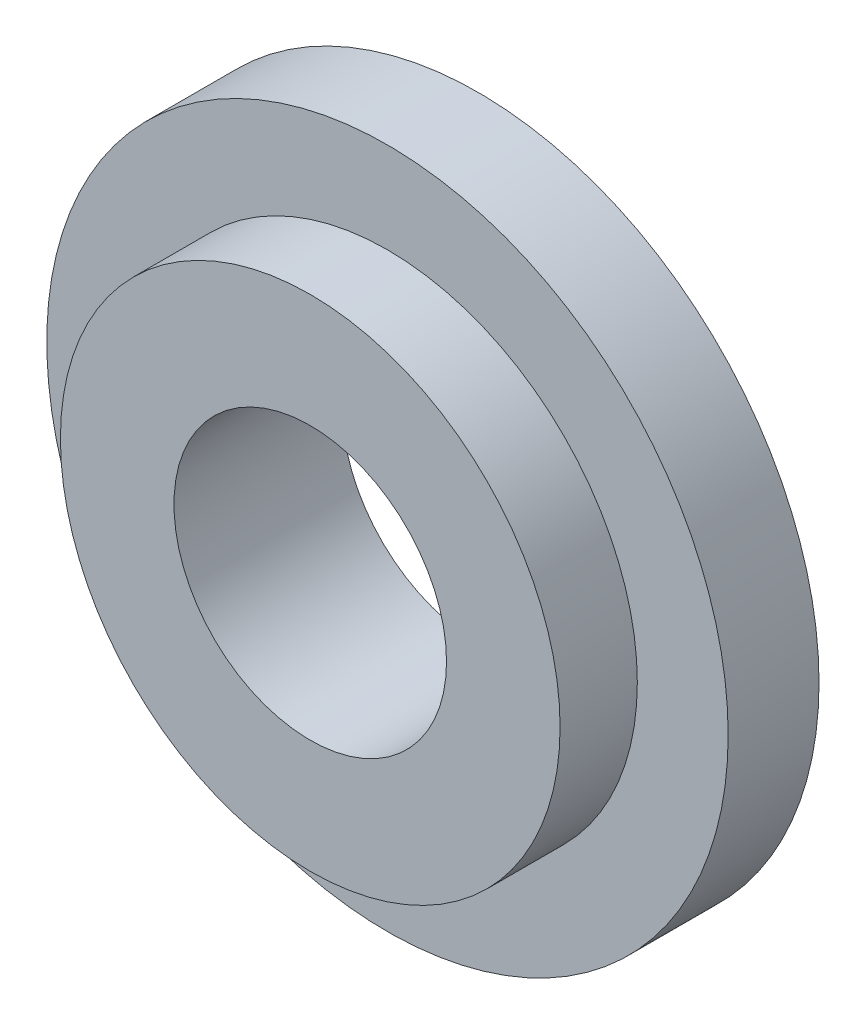
SolidWorks part; units mm, degrees
ref_plane "Front Plane" through (0, 0, 0) normal (0, 0, 1) x (1, 0, 0)
ref_plane "Top Plane" through (0, 0, 0) normal (0, 1, 0) x (1, 0, 0)
ref_plane "Right Plane" through (0, 0, 0) normal (1, 0, 0) x (0, 0, -1)
sketch "Sketch1" plane through (0, 0, 0) normal (0, 0, 1) x (1, 0, 0)
  circle A0 centre (0, 0) radius 3.75
  dimension "D1" = 7.5
extrude "Boss-Extrude1" add sketch "Sketch1" along normal blind 1
sketch "Sketch2" plane through (0, 0, 1) normal (0, 0, 1) x (1, 0, 0)
  circle A0 centre (0, 0) radius 2.75
  dimension "D1" = 5.5
extrude "Boss-Extrude2" add sketch "Sketch2" along normal blind 0.85
sketch "Sketch3" plane through (0, 0, 1.85) normal (0, 0, 1) x (1, 0, 0)
  circle A0 centre (0, 0) radius 1.5
  dimension "D1" = 3
extrude "Cut-Extrude1" cut sketch "Sketch3" against normal through all
